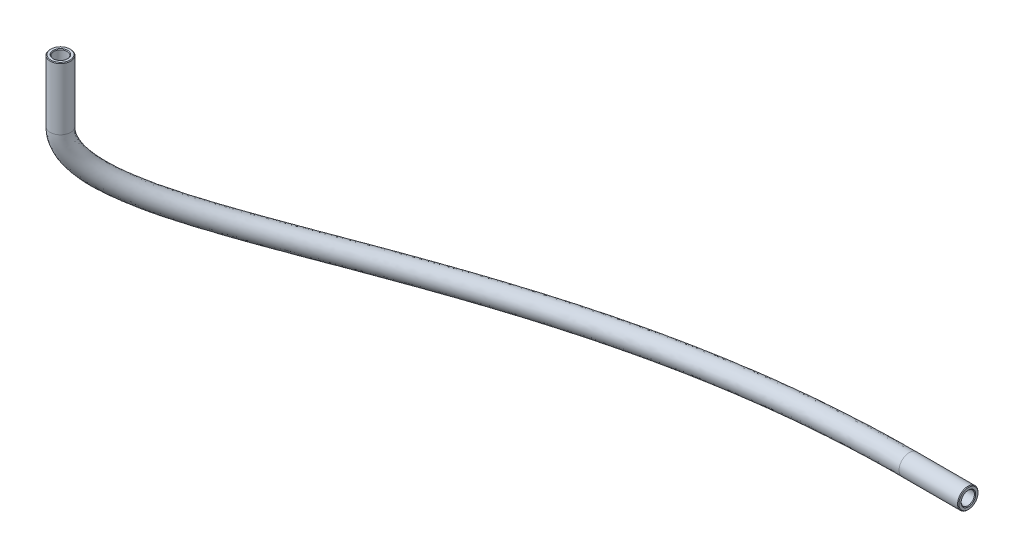
SolidWorks part; units mm, degrees
ref_plane "Front Plane" through (0, 0, 0) normal (0, 0, 1) x (1, 0, 0)
ref_plane "Top Plane" through (0, 0, 0) normal (0, 1, 0) x (1, 0, 0)
ref_plane "Right Plane" through (0, 0, 0) normal (1, 0, 0) x (0, 0, -1)
sketch3d "3DSketch1"
  line L0 (249.105, -102.4823, -40.125) -> (237.525, -102.4823, -40.125)
  line L1 (125.325, -62.125, 13.85) -> (125.325, -74.325, 13.85)
  spline S0 degree 3 poles (237.525, -102.4823, -40.125) (198.5313, -102.4823, -40.125) (145.9414, -97.0294, -13.1375) (125.325, -83.1251, 13.85) (125.325, -74.325, 13.85) knots 0 0 0 0 0.517444 1 1 1 1
sketch "Sketch1" plane through (239.725, 0, 0) normal (-1, 0, 0) x (0, 0, 1)
  circle A0 centre (-40.125, -102.4823) radius 2
  circle A1 centre (-40.125, -102.4823) radius 1.3
  circle A2 centre (-40.125, -102.4823) radius 3.68 construction
  dimension "D1" = 2.6
  dimension "D2" = 4
sweep "Sweep1" add profiles "Sketch1" path "3DSketch1"
chamfer "Chamfer1" distance 0.127 angle 45 4 edges at (249.105, -104.4823, -40.125) (249.105, -103.7823, -40.125) (124.6028, -62.125, 15.715) (124.8556, -62.125, 15.0623)
